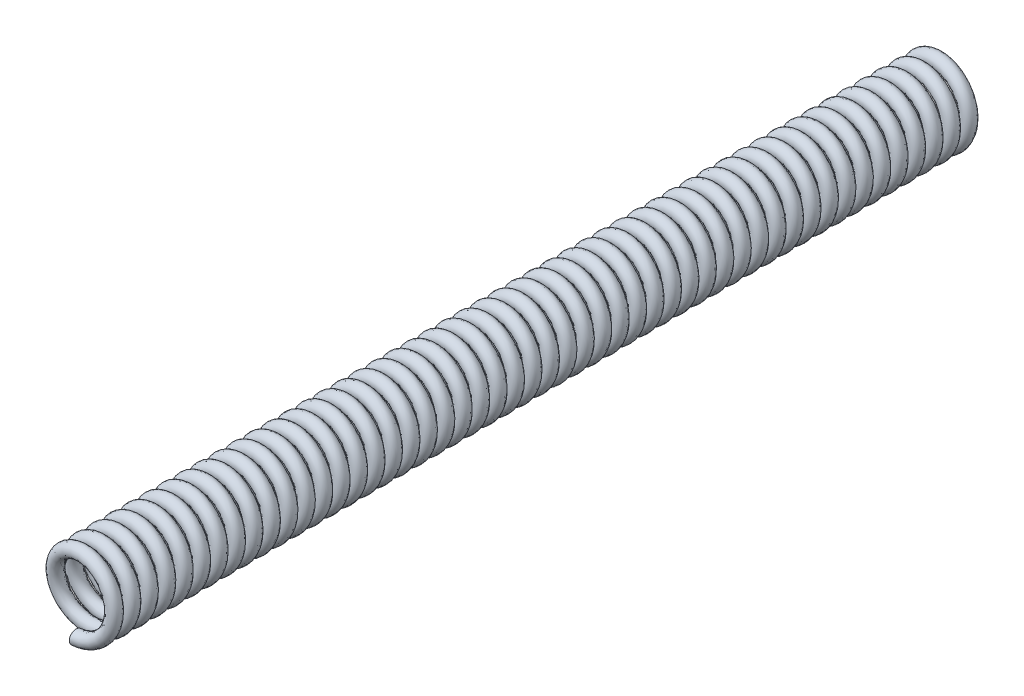
SolidWorks part; units mm, degrees
other "Markup1"
sketch "Sketch3" plane through (-1.5398, -1.3335, -0.1905) normal (-0.3171, -0.6862, -0.6546) x (-0.6897, -0.3069, 0.6558)
material "Chrome Stainless Steel"
ref_plane "Front Plane" through (0, 0, 0) normal (0, 0, 1) x (1, 0, 0)
ref_plane "Top Plane" through (0, 0, 0) normal (0, 1, 0) x (1, 0, 0)
ref_plane "Right Plane" through (0, 0, 0) normal (1, 0, 0) x (0, 0, -1)
sketch "Sketch1" plane through (0, 0, 0) normal (0, 0, 1) x (1, 0, 0)
  circle A0 centre (0, 0) radius 0.9525
  dimension "D1" = 1.905
curve "Helix/Spiral1" pitch 0.4953 height 24.765 turns 50 parameters "LENGTH D3"=24.765
sketch "Sketch2" plane through (0, 0, 0) normal (1, 0, 0) x (0, 0, -1)
  circle A0 centre (0, -0.9525) radius 0.1905
  spline S0 degree 3 poles (0, -0.9525) (-0.0103, -0.9525) (-0.031, -0.9029) (-0.0619, -0.6911) (-0.1032, -0.2683) (-0.1445, 0.2683) (-0.1857, 0.6911) (-0.2167, 0.9029) (-0.2476, 0.9773) (-0.2786, 0.9029) (-0.3096, 0.6911) (-0.3508, 0.2683) (-0.3921, -0.2683) (-0.4334, -0.6911) (-0.4643, -0.9029) (-0.4953, -0.9773) (-0.5263, -0.9029) (-0.5572, -0.6911) (-0.5985, -0.2683) (-0.6398, 0.2683) (-0.681, 0.6911) (-0.712, 0.9029) (-0.743, 0.9773) (-0.7739, 0.9029) (-0.8049, 0.6911) (-0.8461, 0.2683) (-0.8874, -0.2683) (-0.9287, -0.6911) (-0.9596, -0.9029) (-0.9906, -0.9773) (-1.0216, -0.9029) (-1.0525, -0.6911) (-1.0938, -0.2683) (-1.1351, 0.2683) (-1.1763, 0.6911) (-1.2073, 0.9029) (-1.2383, 0.9773) (-1.2692, 0.9029) (-1.3002, 0.6911) (-1.3414, 0.2683) (-1.3827, -0.2683) (-1.424, -0.6911) (-1.4549, -0.9029) (-1.4859, -0.9773) (-1.5169, -0.9029) (-1.5478, -0.6911) (-1.5891, -0.2683) (-1.6304, 0.2683) (-1.6716, 0.6911) (-1.7026, 0.9029) (-1.7336, 0.9773) (-1.7645, 0.9029) (-1.7955, 0.6911) (-1.8367, 0.2683) (-1.878, -0.2683) (-1.9193, -0.6911) (-1.9502, -0.9029) (-1.9812, -0.9773) (-2.0122, -0.9029) (-2.0431, -0.6911) (-2.0844, -0.2683) (-2.1257, 0.2683) (-2.1669, 0.6911) (-2.1979, 0.9029) (-2.2288, 0.9773) (-2.2598, 0.9029) (-2.2908, 0.6911) (-2.332, 0.2683) (-2.3733, -0.2683) (-2.4146, -0.6911) (-2.4455, -0.9029) (-2.4765, -0.9773) (-2.5075, -0.9029) (-2.5384, -0.6911) (-2.5797, -0.2683) (-2.621, 0.2683) (-2.6622, 0.6911) (-2.6932, 0.9029) (-2.7241, 0.9773) (-2.7551, 0.9029) (-2.7861, 0.6911) (-2.8273, 0.2683) (-2.8686, -0.2683) (-2.9099, -0.6911) (-2.9408, -0.9029) (-2.9718, -0.9773) (-3.0028, -0.9029) (-3.0337, -0.6911) (-3.075, -0.2683) (-3.1163, 0.2683) (-3.1575, 0.6911) (-3.1885, 0.9029) (-3.2194, 0.9773) (-3.2504, 0.9029) (-3.2814, 0.6911) (-3.3226, 0.2683) (-3.3639, -0.2683) (-3.4052, -0.6911) (-3.4361, -0.9029) (-3.4671, -0.9773) (-3.4981, -0.9029) (-3.529, -0.6911) (-3.5703, -0.2683) (-3.6116, 0.2683) (-3.6528, 0.6911) (-3.6838, 0.9029) (-3.7147, 0.9773) (-3.7457, 0.9029) (-3.7767, 0.6911) (-3.8179, 0.2683) (-3.8592, -0.2683) (-3.9005, -0.6911) (-3.9314, -0.9029) (-3.9624, -0.9773) (-3.9934, -0.9029) (-4.0243, -0.6911) (-4.0656, -0.2683) (-4.1069, 0.2683) (-4.1481, 0.6911) (-4.1791, 0.9029) (-4.21, 0.9773) (-4.241, 0.9029) (-4.272, 0.6911) (-4.3132, 0.2683) (-4.3545, -0.2683) (-4.3958, -0.6911) (-4.4267, -0.9029) (-4.4577, -0.9773) (-4.4887, -0.9029) (-4.5196, -0.6911) (-4.5609, -0.2683) (-4.6022, 0.2683) (-4.6434, 0.6911) (-4.6744, 0.9029) (-4.7053, 0.9773) (-4.7363, 0.9029) (-4.7673, 0.6911) (-4.8085, 0.2683) (-4.8498, -0.2683) (-4.8911, -0.6911) (-4.922, -0.9029) (-4.953, -0.9773) (-4.984, -0.9029) (-5.0149, -0.6911) (-5.0562, -0.2683) (-5.0975, 0.2683) (-5.1387, 0.6911) (-5.1697, 0.9029) (-5.2007, 0.9773) (-5.2316, 0.9029) (-5.2626, 0.6911) (-5.3038, 0.2683) (-5.3451, -0.2683) (-5.3864, -0.6911) (-5.4173, -0.9029) (-5.4483, -0.9773) (-5.4793, -0.9029) (-5.5102, -0.6911) (-5.5515, -0.2683) (-5.5928, 0.2683) (-5.634, 0.6911) (-5.665, 0.9029) (-5.696, 0.9773) (-5.7269, 0.9029) (-5.7579, 0.6911) (-5.7991, 0.2683) (-5.8404, -0.2683) (-5.8817, -0.6911) (-5.9126, -0.9029) (-5.9436, -0.9773) (-5.9746, -0.9029) (-6.0055, -0.6911) (-6.0468, -0.2683) (-6.0881, 0.2683) (-6.1293, 0.6911) (-6.1603, 0.9029) (-6.1913, 0.9773) (-6.2222, 0.9029) (-6.2532, 0.6911) (-6.2944, 0.2683) (-6.3357, -0.2683) (-6.377, -0.6911) (-6.4079, -0.9029) (-6.4389, -0.9773) (-6.4699, -0.9029) (-6.5008, -0.6911) (-6.5421, -0.2683) (-6.5834, 0.2683) (-6.6246, 0.6911) (-6.6556, 0.9029) (-6.6866, 0.9773) (-6.7175, 0.9029) (-6.7485, 0.6911) (-6.7897, 0.2683) (-6.831, -0.2683) (-6.8723, -0.6911) (-6.9032, -0.9029) (-6.9342, -0.9773) (-6.9652, -0.9029) (-6.9961, -0.6911) (-7.0374, -0.2683) (-7.0787, 0.2683) (-7.1199, 0.6911) (-7.1509, 0.9029) (-7.1819, 0.9773) (-7.2128, 0.9029) (-7.2438, 0.6911) (-7.285, 0.2683) (-7.3263, -0.2683) (-7.3676, -0.6911) (-7.3985, -0.9029) (-7.4295, -0.9773) (-7.4605, -0.9029) (-7.4914, -0.6911) (-7.5327, -0.2683) (-7.574, 0.2683) (-7.6152, 0.6911) (-7.6462, 0.9029) (-7.6772, 0.9773) (-7.7081, 0.9029) (-7.7391, 0.6911) (-7.7803, 0.2683) (-7.8216, -0.2683) (-7.8629, -0.6911) (-7.8938, -0.9029) (-7.9248, -0.9773) (-7.9558, -0.9029) (-7.9867, -0.6911) (-8.028, -0.2683) (-8.0693, 0.2683) (-8.1105, 0.6911) (-8.1415, 0.9029) (-8.1725, 0.9773) (-8.2034, 0.9029) (-8.2344, 0.6911) (-8.2756, 0.2683) (-8.3169, -0.2683) (-8.3582, -0.6911) (-8.3891, -0.9029) (-8.4201, -0.9773) (-8.4511, -0.9029) (-8.482, -0.6911) (-8.5233, -0.2683) (-8.5646, 0.2683) (-8.6058, 0.6911) (-8.6368, 0.9029) (-8.6678, 0.9773) (-8.6987, 0.9029) (-8.7297, 0.6911) (-8.7709, 0.2683) (-8.8122, -0.2683) (-8.8535, -0.6911) (-8.8844, -0.9029) (-8.9154, -0.9773) (-8.9464, -0.9029) (-8.9773, -0.6911) (-9.0186, -0.2683) (-9.0599, 0.2683) (-9.1011, 0.6911) (-9.1321, 0.9029) (-9.1631, 0.9773) (-9.194, 0.9029) (-9.225, 0.6911) (-9.2662, 0.2683) (-9.3075, -0.2683) (-9.3488, -0.6911) (-9.3797, -0.9029) (-9.4107, -0.9773) (-9.4417, -0.9029) (-9.4726, -0.6911) (-9.5139, -0.2683) (-9.5552, 0.2683) (-9.5964, 0.6911) (-9.6274, 0.9029) (-9.6584, 0.9773) (-9.6893, 0.9029) (-9.7203, 0.6911) (-9.7615, 0.2683) (-9.8028, -0.2683) (-9.8441, -0.6911) (-9.875, -0.9029) (-9.906, -0.9773) (-9.937, -0.9029) (-9.9679, -0.6911) (-10.0092, -0.2683) (-10.0505, 0.2683) (-10.0917, 0.6911) (-10.1227, 0.9029) (-10.1537, 0.9773) (-10.1846, 0.9029) (-10.2156, 0.6911) (-10.2568, 0.2683) (-10.2981, -0.2683) (-10.3394, -0.6911) (-10.3703, -0.9029) (-10.4013, -0.9773) (-10.4323, -0.9029) (-10.4632, -0.6911) (-10.5045, -0.2683) (-10.5458, 0.2683) (-10.587, 0.6911) (-10.618, 0.9029) (-10.649, 0.9773) (-10.6799, 0.9029) (-10.7109, 0.6911) (-10.7521, 0.2683) (-10.7934, -0.2683) (-10.8347, -0.6911) (-10.8656, -0.9029) (-10.8966, -0.9773) (-10.9276, -0.9029) (-10.9585, -0.6911) (-10.9998, -0.2683) (-11.0411, 0.2683) (-11.0823, 0.6911) (-11.1133, 0.9029) (-11.1443, 0.9773) (-11.1752, 0.9029) (-11.2062, 0.6911) (-11.2474, 0.2683) (-11.2887, -0.2683) (-11.33, -0.6911) (-11.3609, -0.9029) (-11.3919, -0.9773) (-11.4229, -0.9029) (-11.4538, -0.6911) (-11.4951, -0.2683) (-11.5364, 0.2683) (-11.5776, 0.6911) (-11.6086, 0.9029) (-11.6396, 0.9773) (-11.6705, 0.9029) (-11.7015, 0.6911) (-11.7427, 0.2683) (-11.784, -0.2683) (-11.8253, -0.6911) (-11.8562, -0.9029) (-11.8872, -0.9773) (-11.9182, -0.9029) (-11.9491, -0.6911) (-11.9904, -0.2683) (-12.0317, 0.2683) (-12.0729, 0.6911) (-12.1039, 0.9029) (-12.1349, 0.9773) (-12.1658, 0.9029) (-12.1968, 0.6911) (-12.238, 0.2683) (-12.2793, -0.2683) (-12.3206, -0.6911) (-12.3515, -0.9029) (-12.3825, -0.9773) (-12.4135, -0.9029) (-12.4444, -0.6911) (-12.4857, -0.2683) (-12.527, 0.2683) (-12.5682, 0.6911) (-12.5992, 0.9029) (-12.6302, 0.9773) (-12.6611, 0.9029) (-12.6921, 0.6911) (-12.7333, 0.2683) (-12.7746, -0.2683) (-12.8159, -0.6911) (-12.8468, -0.9029) (-12.8778, -0.9773) (-12.9088, -0.9029) (-12.9397, -0.6911) (-12.981, -0.2683) (-13.0223, 0.2683) (-13.0635, 0.6911) (-13.0945, 0.9029) (-13.1255, 0.9773) (-13.1564, 0.9029) (-13.1874, 0.6911) (-13.2286, 0.2683) (-13.2699, -0.2683) (-13.3112, -0.6911) (-13.3421, -0.9029) (-13.3731, -0.9773) (-13.4041, -0.9029) (-13.435, -0.6911) (-13.4763, -0.2683) (-13.5176, 0.2683) (-13.5588, 0.6911) (-13.5898, 0.9029) (-13.6208, 0.9773) (-13.6517, 0.9029) (-13.6827, 0.6911) (-13.7239, 0.2683) (-13.7652, -0.2683) (-13.8065, -0.6911) (-13.8374, -0.9029) (-13.8684, -0.9773) (-13.8994, -0.9029) (-13.9303, -0.6911) (-13.9716, -0.2683) (-14.0129, 0.2683) (-14.0541, 0.6911) (-14.0851, 0.9029) (-14.1161, 0.9773) (-14.147, 0.9029) (-14.178, 0.6911) (-14.2192, 0.2683) (-14.2605, -0.2683) (-14.3018, -0.6911) (-14.3327, -0.9029) (-14.3637, -0.9773) (-14.3947, -0.9029) (-14.4256, -0.6911) (-14.4669, -0.2683) (-14.5082, 0.2683) (-14.5494, 0.6911) (-14.5804, 0.9029) (-14.6114, 0.9773) (-14.6423, 0.9029) (-14.6733, 0.6911) (-14.7145, 0.2683) (-14.7558, -0.2683) (-14.7971, -0.6911) (-14.828, -0.9029) (-14.859, -0.9773) (-14.89, -0.9029) (-14.9209, -0.6911) (-14.9622, -0.2683) (-15.0035, 0.2683) (-15.0447, 0.6911) (-15.0757, 0.9029) (-15.1067, 0.9773) (-15.1376, 0.9029) (-15.1686, 0.6911) (-15.2098, 0.2683) (-15.2511, -0.2683) (-15.2924, -0.6911) (-15.3233, -0.9029) (-15.3543, -0.9773) (-15.3853, -0.9029) (-15.4162, -0.6911) (-15.4575, -0.2683) (-15.4988, 0.2683) (-15.54, 0.6911) (-15.571, 0.9029) (-15.602, 0.9773) (-15.6329, 0.9029) (-15.6639, 0.6911) (-15.7051, 0.2683) (-15.7464, -0.2683) (-15.7877, -0.6911) (-15.8186, -0.9029) (-15.8496, -0.9773) (-15.8806, -0.9029) (-15.9115, -0.6911) (-15.9528, -0.2683) (-15.9941, 0.2683) (-16.0353, 0.6911) (-16.0663, 0.9029) (-16.0973, 0.9773) (-16.1282, 0.9029) (-16.1592, 0.6911) (-16.2004, 0.2683) (-16.2417, -0.2683) (-16.283, -0.6911) (-16.3139, -0.9029) (-16.3449, -0.9773) (-16.3759, -0.9029) (-16.4068, -0.6911) (-16.4481, -0.2683) (-16.4894, 0.2683) (-16.5306, 0.6911) (-16.5616, 0.9029) (-16.5926, 0.9773) (-16.6235, 0.9029) (-16.6545, 0.6911) (-16.6957, 0.2683) (-16.737, -0.2683) (-16.7783, -0.6911) (-16.8092, -0.9029) (-16.8402, -0.9773) (-16.8712, -0.9029) (-16.9021, -0.6911) (-16.9434, -0.2683) (-16.9847, 0.2683) (-17.0259, 0.6911) (-17.0569, 0.9029) (-17.0879, 0.9773) (-17.1188, 0.9029) (-17.1498, 0.6911) (-17.191, 0.2683) (-17.2323, -0.2683) (-17.2736, -0.6911) (-17.3045, -0.9029) (-17.3355, -0.9773) (-17.3665, -0.9029) (-17.3974, -0.6911) (-17.4387, -0.2683) (-17.48, 0.2683) (-17.5212, 0.6911) (-17.5522, 0.9029) (-17.5831, 0.9773) (-17.6141, 0.9029) (-17.6451, 0.6911) (-17.6863, 0.2683) (-17.7276, -0.2683) (-17.7689, -0.6911) (-17.7998, -0.9029) (-17.8308, -0.9773) (-17.8618, -0.9029) (-17.8927, -0.6911) (-17.934, -0.2683) (-17.9753, 0.2683) (-18.0165, 0.6911) (-18.0475, 0.9029) (-18.0784, 0.9773) (-18.1094, 0.9029) (-18.1404, 0.6911) (-18.1816, 0.2683) (-18.2229, -0.2683) (-18.2642, -0.6911) (-18.2951, -0.9029) (-18.3261, -0.9773) (-18.3571, -0.9029) (-18.388, -0.6911) (-18.4293, -0.2683) (-18.4706, 0.2683) (-18.5118, 0.6911) (-18.5428, 0.9029) (-18.5737, 0.9773) (-18.6047, 0.9029) (-18.6357, 0.6911) (-18.6769, 0.2683) (-18.7182, -0.2683) (-18.7595, -0.6911) (-18.7904, -0.9029) (-18.8214, -0.9773) (-18.8524, -0.9029) (-18.8833, -0.6911) (-18.9246, -0.2683) (-18.9659, 0.2683) (-19.0071, 0.6911) (-19.0381, 0.9029) (-19.069, 0.9773) (-19.1, 0.9029) (-19.131, 0.6911) (-19.1722, 0.2683) (-19.2135, -0.2683) (-19.2548, -0.6911) (-19.2857, -0.9029) (-19.3167, -0.9773) (-19.3477, -0.9029) (-19.3786, -0.6911) (-19.4199, -0.2683) (-19.4612, 0.2683) (-19.5024, 0.6911) (-19.5334, 0.9029) (-19.5643, 0.9773) (-19.5953, 0.9029) (-19.6263, 0.6911) (-19.6675, 0.2683) (-19.7088, -0.2683) (-19.7501, -0.6911) (-19.781, -0.9029) (-19.812, -0.9773) (-19.843, -0.9029) (-19.8739, -0.6911) (-19.9152, -0.2683) (-19.9565, 0.2683) (-19.9977, 0.6911) (-20.0287, 0.9029) (-20.0596, 0.9773) (-20.0906, 0.9029) (-20.1216, 0.6911) (-20.1628, 0.2683) (-20.2041, -0.2683) (-20.2454, -0.6911) (-20.2763, -0.9029) (-20.3073, -0.9773) (-20.3383, -0.9029) (-20.3692, -0.6911) (-20.4105, -0.2683) (-20.4518, 0.2683) (-20.493, 0.6911) (-20.524, 0.9029) (-20.5549, 0.9773) (-20.5859, 0.9029) (-20.6169, 0.6911) (-20.6581, 0.2683) (-20.6994, -0.2683) (-20.7407, -0.6911) (-20.7716, -0.9029) (-20.8026, -0.9773) (-20.8336, -0.9029) (-20.8645, -0.6911) (-20.9058, -0.2683) (-20.9471, 0.2683) (-20.9883, 0.6911) (-21.0193, 0.9029) (-21.0502, 0.9773) (-21.0812, 0.9029) (-21.1122, 0.6911) (-21.1534, 0.2683) (-21.1947, -0.2683) (-21.236, -0.6911) (-21.2669, -0.9029) (-21.2979, -0.9773) (-21.3289, -0.9029) (-21.3598, -0.6911) (-21.4011, -0.2683) (-21.4424, 0.2683) (-21.4836, 0.6911) (-21.5146, 0.9029) (-21.5455, 0.9773) (-21.5765, 0.9029) (-21.6075, 0.6911) (-21.6487, 0.2683) (-21.69, -0.2683) (-21.7313, -0.6911) (-21.7622, -0.9029) (-21.7932, -0.9773) (-21.8242, -0.9029) (-21.8551, -0.6911) (-21.8964, -0.2683) (-21.9377, 0.2683) (-21.9789, 0.6911) (-22.0099, 0.9029) (-22.0408, 0.9773) (-22.0718, 0.9029) (-22.1028, 0.6911) (-22.144, 0.2683) (-22.1853, -0.2683) (-22.2266, -0.6911) (-22.2575, -0.9029) (-22.2885, -0.9773) (-22.3195, -0.9029) (-22.3504, -0.6911) (-22.3917, -0.2683) (-22.433, 0.2683) (-22.4742, 0.6911) (-22.5052, 0.9029) (-22.5361, 0.9773) (-22.5671, 0.9029) (-22.5981, 0.6911) (-22.6393, 0.2683) (-22.6806, -0.2683) (-22.7219, -0.6911) (-22.7528, -0.9029) (-22.7838, -0.9773) (-22.8148, -0.9029) (-22.8457, -0.6911) (-22.887, -0.2683) (-22.9283, 0.2683) (-22.9695, 0.6911) (-23.0005, 0.9029) (-23.0314, 0.9773) (-23.0624, 0.9029) (-23.0934, 0.6911) (-23.1346, 0.2683) (-23.1759, -0.2683) (-23.2172, -0.6911) (-23.2481, -0.9029) (-23.2791, -0.9773) (-23.3101, -0.9029) (-23.341, -0.6911) (-23.3823, -0.2683) (-23.4236, 0.2683) (-23.4648, 0.6911) (-23.4958, 0.9029) (-23.5267, 0.9773) (-23.5577, 0.9029) (-23.5887, 0.6911) (-23.6299, 0.2683) (-23.6712, -0.2683) (-23.7125, -0.6911) (-23.7434, -0.9029) (-23.7744, -0.9773) (-23.8054, -0.9029) (-23.8363, -0.6911) (-23.8776, -0.2683) (-23.9189, 0.2683) (-23.9601, 0.6911) (-23.9911, 0.9029) (-24.022, 0.9773) (-24.053, 0.9029) (-24.084, 0.6911) (-24.1252, 0.2683) (-24.1665, -0.2683) (-24.2078, -0.6911) (-24.2387, -0.9029) (-24.2697, -0.9773) (-24.3007, -0.9029) (-24.3316, -0.6911) (-24.3729, -0.2683) (-24.4142, 0.2683) (-24.4554, 0.6911) (-24.4864, 0.9029) (-24.5174, 0.9773) (-24.5483, 0.9029) (-24.5793, 0.6911) (-24.6205, 0.2683) (-24.6618, -0.2683) (-24.7031, -0.6911) (-24.734, -0.9029) (-24.7547, -0.9525) (-24.765, -0.9525) knots 0 0 0 0 0.00125 0.0025 0.00375 0.00625 0.0075 0.00875 0.01 0.01125 0.0125 0.01375 0.01625 0.0175 0.01875 0.02 0.02125 0.0225 0.02375 0.02625 0.0275 0.02875 0.03 0.03125 0.0325 0.03375 0.03625 0.0375 0.03875 0.04 0.04125 0.0425 0.04375 0.04625 0.0475 0.04875 0.05 0.05125 0.0525 0.05375 0.05625 0.0575 0.05875 0.06 0.06125 0.0625 0.06375 0.06625 0.0675 0.06875 0.07 0.07125 0.0725 0.07375 0.07625 0.0775 0.07875 0.08 0.08125 0.0825 0.08375 0.08625 0.0875 0.08875 0.09 0.09125 0.0925 0.09375 0.09625 0.0975 0.09875 0.1 0.10125 0.1025 0.10375 0.10625 0.1075 0.10875 0.11 0.11125 0.1125 0.11375 0.11625 0.1175 0.11875 0.12 0.12125 0.1225 0.12375 0.12625 0.1275 0.12875 0.13 0.13125 0.1325 0.13375 0.13625 0.1375 0.13875 0.14 0.14125 0.1425 0.14375 0.14625 0.1475 0.14875 0.15 0.15125 0.1525 0.15375 0.15625 0.1575 0.15875 0.16 0.16125 0.1625 0.16375 0.16625 0.1675 0.16875 0.17 0.17125 0.1725 0.17375 0.17625 0.1775 0.17875 0.18 0.18125 0.1825 0.18375 0.18625 0.1875 0.18875 0.19 0.19125 0.1925 0.19375 0.19625 0.1975 0.19875 0.2 0.20125 0.2025 0.20375 0.20625 0.2075 0.20875 0.21 0.21125 0.2125 0.21375 0.21625 0.2175 0.21875 0.22 0.22125 0.2225 0.22375 0.22625 0.2275 0.22875 0.23 0.23125 0.2325 0.23375 0.23625 0.2375 0.23875 0.24 0.24125 0.2425 0.24375 0.24625 0.2475 0.24875 0.25 0.25125 0.2525 0.25375 0.25625 0.2575 0.25875 0.26 0.26125 0.2625 0.26375 0.26625 0.2675 0.26875 0.27 0.27125 0.2725 0.27375 0.27625 0.2775 0.27875 0.28 0.28125 0.2825 0.28375 0.28625 0.2875 0.28875 0.29 0.29125 0.2925 0.29375 0.29625 0.2975 0.29875 0.3 0.30125 0.3025 0.30375 0.30625 0.3075 0.30875 0.31 0.31125 0.3125 0.31375 0.31625 0.3175 0.31875 0.32 0.32125 0.3225 0.32375 0.32625 0.3275 0.32875 0.33 0.33125 0.3325 0.33375 0.33625 0.3375 0.33875 0.34 0.34125 0.3425 0.34375 0.34625 0.3475 0.34875 0.35 0.35125 0.3525 0.35375 0.35625 0.3575 0.35875 0.36 0.36125 0.3625 0.36375 0.36625 0.3675 0.36875 0.37 0.37125 0.3725 0.37375 0.37625 0.3775 0.37875 0.38 0.38125 0.3825 0.38375 0.38625 0.3875 0.38875 0.39 0.39125 0.3925 0.39375 0.39625 0.3975 0.39875 0.4 0.40125 0.4025 0.40375 0.40625 0.4075 0.40875 0.41 0.41125 0.4125 0.41375 0.41625 0.4175 0.41875 0.42 0.42125 0.4225 0.42375 0.42625 0.4275 0.42875 0.43 0.43125 0.4325 0.43375 0.43625 0.4375 0.43875 0.44 0.44125 0.4425 0.44375 0.44625 0.4475 0.44875 0.45 0.45125 0.4525 0.45375 0.45625 0.4575 0.45875 0.46 0.46125 0.4625 0.46375 0.46625 0.4675 0.46875 0.47 0.47125 0.4725 0.47375 0.47625 0.4775 0.47875 0.48 0.48125 0.4825 0.48375 0.48625 0.4875 0.48875 0.49 0.49125 0.4925 0.49375 0.49625 0.4975 0.49875 0.5 0.50125 0.5025 0.50375 0.50625 0.5075 0.50875 0.51 0.51125 0.5125 0.51375 0.51625 0.5175 0.51875 0.52 0.52125 0.5225 0.52375 0.52625 0.5275 0.52875 0.53 0.53125 0.5325 0.53375 0.53625 0.5375 0.53875 0.54 0.54125 0.5425 0.54375 0.54625 0.5475 0.54875 0.55 0.55125 0.5525 0.55375 0.55625 0.5575 0.55875 0.56 0.56125 0.5625 0.56375 0.56625 0.5675 0.56875 0.57 0.57125 0.5725 0.57375 0.57625 0.5775 0.57875 0.58 0.58125 0.5825 0.58375 0.58625 0.5875 0.58875 0.59 0.59125 0.5925 0.59375 0.59625 0.5975 0.59875 0.6 0.60125 0.6025 0.60375 0.60625 0.6075 0.60875 0.61 0.61125 0.6125 0.61375 0.61625 0.6175 0.61875 0.62 0.62125 0.6225 0.62375 0.62625 0.6275 0.62875 0.63 0.63125 0.6325 0.63375 0.63625 0.6375 0.63875 0.64 0.64125 0.6425 0.64375 0.64625 0.6475 0.64875 0.65 0.65125 0.6525 0.65375 0.65625 0.6575 0.65875 0.66 0.66125 0.6625 0.66375 0.66625 0.6675 0.66875 0.67 0.67125 0.6725 0.67375 0.67625 0.6775 0.67875 0.68 0.68125 0.6825 0.68375 0.68625 0.6875 0.68875 0.69 0.69125 0.6925 0.69375 0.69625 0.6975 0.69875 0.7 0.70125 0.7025 0.70375 0.70625 0.7075 0.70875 0.71 0.71125 0.7125 0.71375 0.71625 0.7175 0.71875 0.72 0.72125 0.7225 0.72375 0.72625 0.7275 0.72875 0.73 0.73125 0.7325 0.73375 0.73625 0.7375 0.73875 0.74 0.74125 0.7425 0.74375 0.74625 0.7475 0.74875 0.75 0.75125 0.7525 0.75375 0.75625 0.7575 0.75875 0.76 0.76125 0.7625 0.76375 0.76625 0.7675 0.76875 0.77 0.77125 0.7725 0.77375 0.77625 0.7775 0.77875 0.78 0.78125 0.7825 0.78375 0.78625 0.7875 0.78875 0.79 0.79125 0.7925 0.79375 0.79625 0.7975 0.79875 0.8 0.80125 0.8025 0.80375 0.80625 0.8075 0.80875 0.81 0.81125 0.8125 0.81375 0.81625 0.8175 0.81875 0.82 0.82125 0.8225 0.82375 0.82625 0.8275 0.82875 0.83 0.83125 0.8325 0.83375 0.83625 0.8375 0.83875 0.84 0.84125 0.8425 0.84375 0.84625 0.8475 0.84875 0.85 0.85125 0.8525 0.85375 0.85625 0.8575 0.85875 0.86 0.86125 0.8625 0.86375 0.86625 0.8675 0.86875 0.87 0.87125 0.8725 0.87375 0.87625 0.8775 0.87875 0.88 0.88125 0.8825 0.88375 0.88625 0.8875 0.88875 0.89 0.89125 0.8925 0.89375 0.89625 0.8975 0.89875 0.9 0.90125 0.9025 0.90375 0.90625 0.9075 0.90875 0.91 0.91125 0.9125 0.91375 0.91625 0.9175 0.91875 0.92 0.92125 0.9225 0.92375 0.92625 0.9275 0.92875 0.93 0.93125 0.9325 0.93375 0.93625 0.9375 0.93875 0.94 0.94125 0.9425 0.94375 0.94625 0.9475 0.94875 0.95 0.95125 0.9525 0.95375 0.95625 0.9575 0.95875 0.96 0.96125 0.9625 0.96375 0.96625 0.9675 0.96875 0.97 0.97125 0.9725 0.97375 0.97625 0.9775 0.97875 0.98 0.98125 0.9825 0.98375 0.98625 0.9875 0.98875 0.99 0.99125 0.9925 0.99375 0.99625 0.9975 0.99875 1 1 1 1 construction
  dimension "D1" = 0.381
sweep "Sweep1" add profiles "Sketch2" path "Helix/Spiral1"
